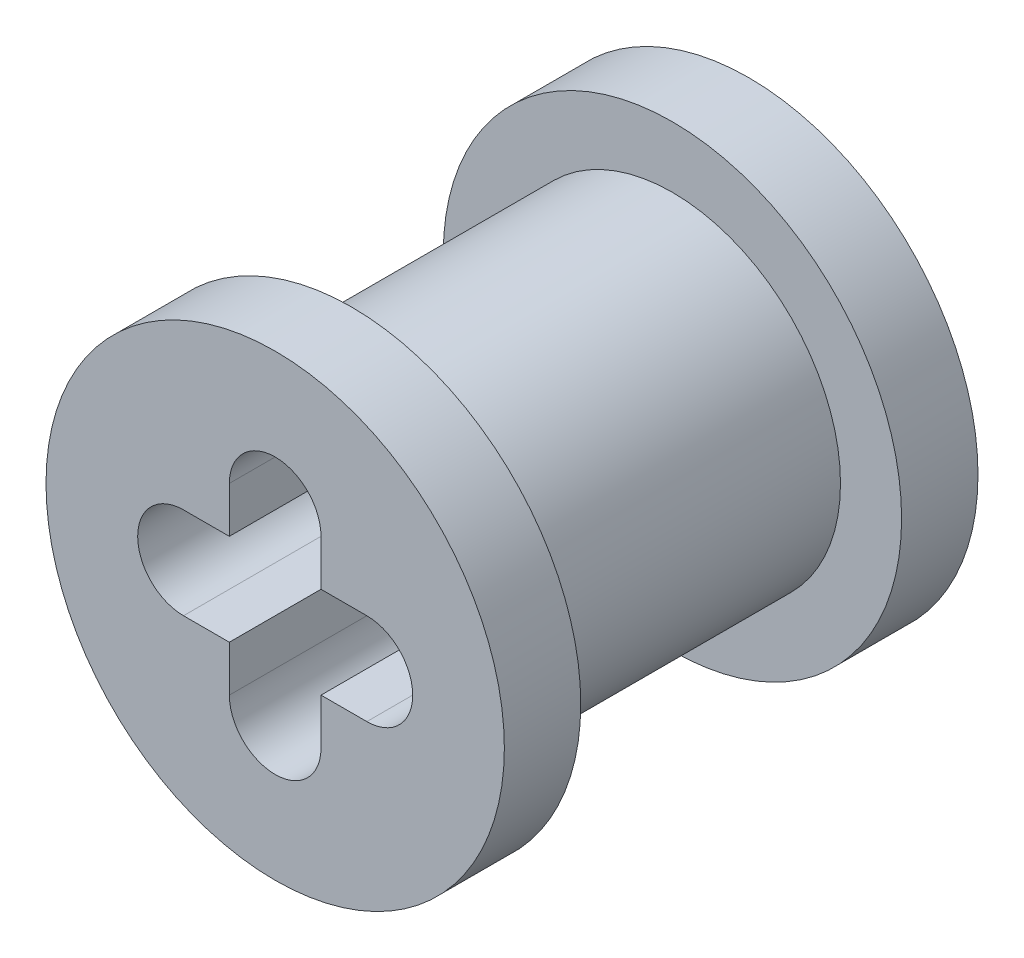
SolidWorks part; units mm, degrees
material "PVC Rigid"
ref_plane "Front Plane" through (0, 0, 0) normal (0, 0, 1) x (1, 0, 0)
ref_plane "Top Plane" through (0, 0, 0) normal (0, 1, 0) x (1, 0, 0)
ref_plane "Right Plane" through (0, 0, 0) normal (1, 0, 0) x (0, 0, -1)
sketch "Sketch1" plane through (0, 0, 0) normal (0, 0, 1) x (1, 0, 0)
  line L0 (-7.874, 0) -> (7.874, 0) construction
  line L1 (6.35, 0) -> (9.398, 0) construction
  line L2 (6.35, 0.762) -> (9.398, 0.762)
  line L10 (6.35, -0.762) -> (9.398, -0.762)
  line L19 (7.874, 1.524) -> (7.874, -1.524) construction
  line L20 (8.636, 1.524) -> (8.636, -1.524)
  line L21 (7.112, 1.524) -> (7.112, -1.524)
  line L22 (6.35, 0) -> (9.398, 0) construction
  circle A0 centre (7.874, 0) radius 2.794
  arc A2 (6.35, 0.762) -> (6.35, -0.762) centre (6.35, 0) ccw
  circle A4 centre (7.874, 0) radius 2.54
  arc A5 (9.398, -0.762) -> (9.398, 0.762) centre (9.398, 0) ccw
  circle A23 centre (7.874, 0) radius 2.286 construction
  arc A24 (8.636, 1.524) -> (7.112, 1.524) centre (7.874, 1.524) ccw
  arc A25 (7.112, -1.524) -> (8.636, -1.524) centre (7.874, -1.524) ccw
  point P13 (9.525, 0)
  point P14 (7.874, 0)
  point P15 (7.62, 0)
  point P17 (0, 3.302)
  point P18 (19.05, 3.302)
  point P19 (0, -3.302)
  point P20 (19.05, -3.302)
  point P23 (13.843, 0)
  point P24 (7.874, 0)
  point P25 (23.368, 0)
  point P26 (3.429, 0)
  point P27 (-7.874, -3.302)
  point P28 (7.874, -3.302)
  point P29 (-7.874, 3.302)
  point P30 (7.874, 3.302)
  point P35 (11.811, 0)
  point P60 (11.5175, 1.1139)
  point P70 (7.874, 0)
  point P77 (7.874, 0)
  dimension "D4" = 5.08
  dimension "D7" = 4.572
  dimension "D8" = 1.524
extrude "Boss-Extrude1" add sketch "Sketch1" along normal blind 3.937
sketch "Sketch2" plane through (0, 0, 0) normal (0, 0, -1) x (-1, 0, 0)
  circle A0 centre (-7.874, 0) radius 2.794
  circle A1 centre (-7.874, 0) radius 3.81
extrude "Boss-Extrude2" add sketch "Sketch2" against normal blind 1.27
ref_plane "Plane1" through (0, 0, 3.937) normal (0, 0, 1) x (1, 0, 0)
mirror "Mirror1" about plane through (0, 0, 3.937) normal (0, 0, 1) of "Boss-Extrude2", "Boss-Extrude1"
